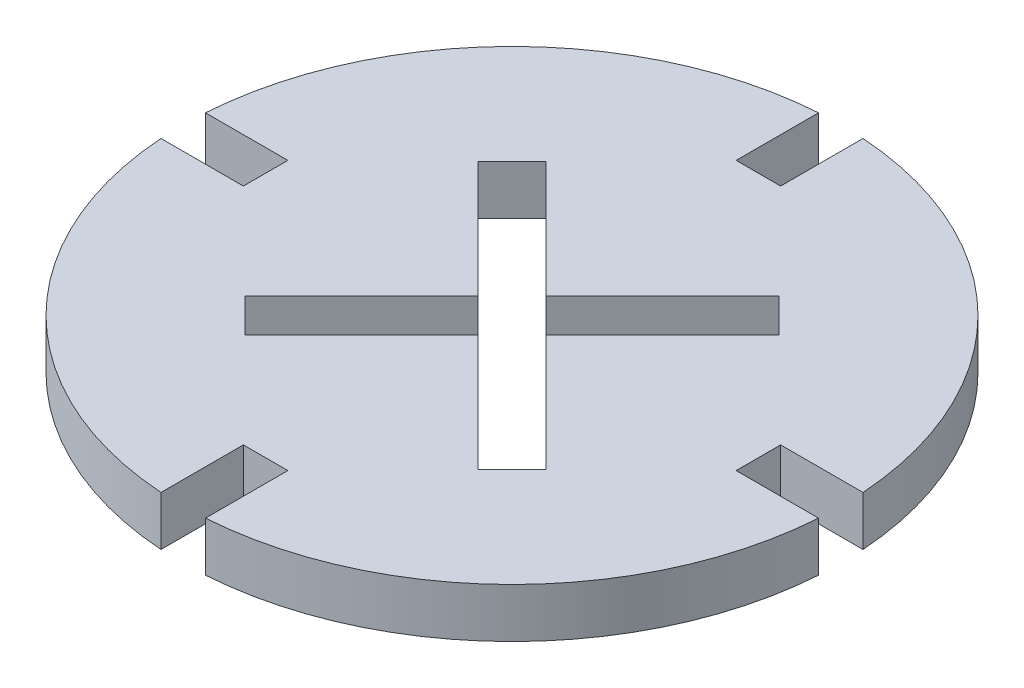
SolidWorks part; units mm, degrees
ref_plane "Alzado" through (0, 0, 0) normal (0, 0, 1) x (1, 0, 0)
ref_plane "Planta" through (0, 0, 0) normal (0, 1, 0) x (1, 0, 0)
ref_plane "Vista lateral" through (0, 0, 0) normal (1, 0, 0) x (0, 0, -1)
sketch "Sketch1" plane through (0, 0, 0) normal (0, 1, 0) x (1, 0, 0)
  line L0 (48.4783, 121.7343) -> (242.3913, 121.7343) construction
  line L22 (0, 18.8238) -> (0, -18.4966) construction
  line L34 (-16.3461, 0) -> (18.4218, 0) construction
  line L37 (1.35, 14.9544) -> (-1.35, 14.9544)
  line L38 (-1.35, 14.9544) -> (-1.35, 19.9544)
  line L39 (-19.9544, 1.35) -> (-14.9544, 1.35)
  line L40 (-14.9544, 1.35) -> (-14.9544, -1.35)
  line L43 (-19.9544, -1.35) -> (-14.9544, -1.35)
  line L44 (1.35, -14.9544) -> (-1.35, -14.9544)
  line L45 (-1.35, -14.9544) -> (-1.35, -19.9544)
  line L46 (1.35, -14.9544) -> (1.35, -19.9544)
  line L47 (19.9544, -1.35) -> (14.9544, -1.35)
  line L48 (14.9544, 1.35) -> (14.9544, -1.35)
  line L49 (19.9544, 1.35) -> (14.9544, 1.35)
  line L50 (1.35, 14.9544) -> (1.35, 19.9544)
  arc A7 (-1.35, 19.9544) -> (-19.9544, 1.35) centre (0, 0) ccw
  arc A8 (-1.35, -19.9544) -> (-19.9544, -1.35) centre (0, 0) cw
  arc A9 (1.35, -19.9544) -> (19.9544, -1.35) centre (0, 0) ccw
  arc A10 (1.35, 19.9544) -> (19.9544, 1.35) centre (0, 0) cw
  point P6 (-14.9544, 0)
  point P19 (0, -14.9544)
  point P26 (0, 14.9544)
extrude "Boss-Extrude1" add sketch "Sketch1" along normal blind 3
sketch "Sketch3" plane through (0, 3, 0) normal (0, 1, 0) x (1, 0, 0)
  line L5 (-14.1421, 14.1421) -> (14.1421, -14.1421) construction
  line L6 (-14.1421, -14.1421) -> (14.1421, 14.1421) construction
  line L9 (0, 2.0506) -> (7.0711, 9.1217)
  line L13 (-9.1217, 7.0711) -> (-7.0711, 9.1217)
  line L14 (0, 2.0506) -> (-7.0711, 9.1217)
  line L15 (7.0711, 9.1217) -> (9.1217, 7.0711)
  line L16 (0, 4.2276) -> (0, -2.8592) construction
  line L17 (-9.1217, -7.0711) -> (-7.0711, -9.1217)
  line L18 (-2.0506, 0) -> (-9.1217, -7.0711)
  line L19 (-2.0506, 0) -> (-9.1217, 7.0711)
  line L20 (2.0506, 0) -> (9.1217, 7.0711)
  line L21 (2.0506, 0) -> (9.1217, -7.0711)
  line L22 (7.0711, -9.1217) -> (9.1217, -7.0711)
  line L23 (0, -2.0506) -> (7.0711, -9.1217)
  line L24 (0, -2.0506) -> (-7.0711, -9.1217)
  arc A0 (-1.35, 19.9544) -> (-19.9544, 1.35) centre (0, 0) ccw construction
  arc A1 (1.35, -19.9544) -> (19.9544, -1.35) centre (0, 0) ccw construction
  arc A2 (19.9544, 1.35) -> (1.35, 19.9544) centre (0, 0) ccw construction
  arc A3 (-19.9544, -1.35) -> (-1.35, -19.9544) centre (0, 0) ccw construction
  point P27 (-8.0964, 8.0964)
  point P28 (8.0964, 8.0964)
  point P35 (-8.0964, -8.0964)
extrude "Cut-Extrude1" cut sketch "Sketch3" against normal up to next
equation "\"material\"= 3"
equation "\"kerf\"= \"material\" - 0.3mm"
equation "\"large\"= 90"
equation "\"Radius\"= 10"
equation "\"D4@Sketch1\"=\"kerf\"/2"
equation "\"D5@Sketch1\"=\"kerf\"/2"
equation "\"D1@Boss-Extrude1\"=\"material\""
equation "\"D3@Sketch3\"=\"subkerf\"/2"
equation "\"D4@Sketch3\"=\"subkerf\"/2"
equation "\"D5@Sketch3\"=\"subkerf\"/2"
equation "\"subkerf\"= \"material\" - 0.1mm"
